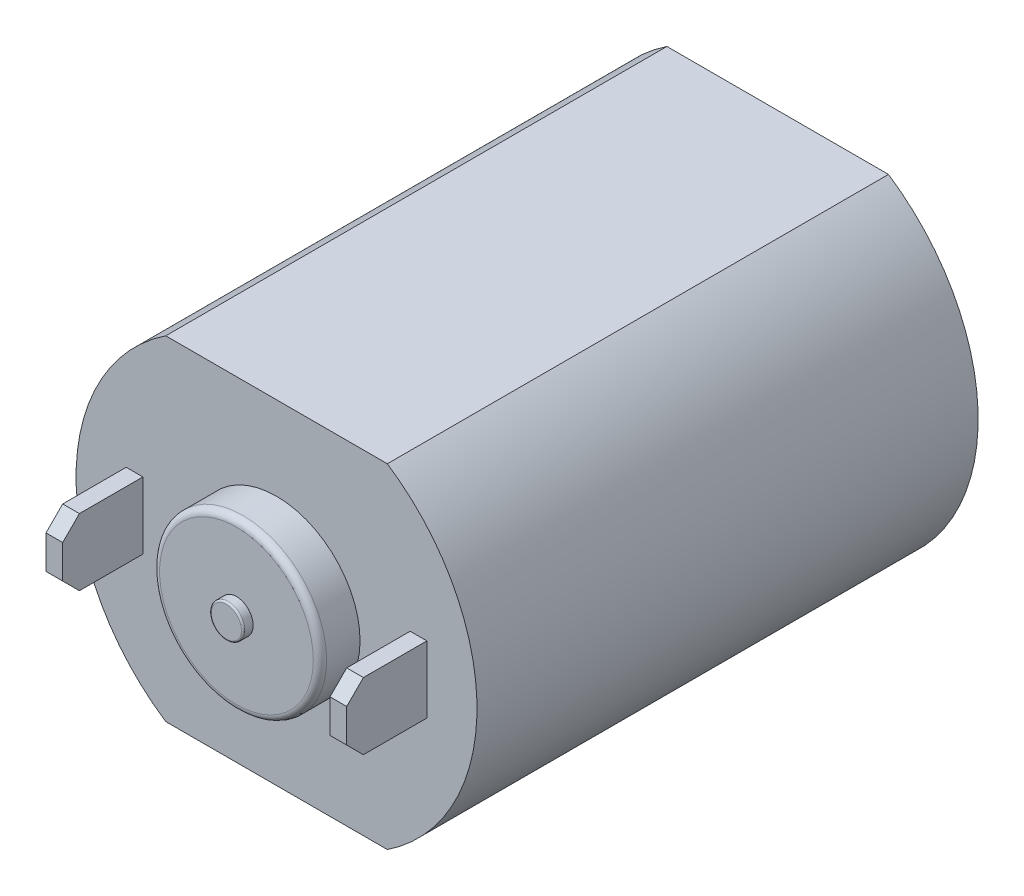
SolidWorks part; units mm, degrees
ref_plane "前视基准面" through (0, 0, 0) normal (0, 0, 1) x (1, 0, 0)
ref_plane "上视基准面" through (0, 0, 0) normal (0, 1, 0) x (1, 0, 0)
ref_plane "右视基准面" through (0, 0, 0) normal (1, 0, 0) x (0, 0, -1)
sketch "草图1" plane through (0, 0, 0) normal (0, 0, 1) x (1, 0, 0)
  circle A0 centre (0, 0) radius 6
extrude "凸台-拉伸1" add sketch "草图1" along normal blind 15 contours A0
sketch "草图6" plane through (0, 0, 0) normal (0, 0, -1) x (-1, 0, 0)
  line L0 (-5.8948, 0) -> (4.7099, 0) construction
  line L1 (-3.3166, 5) -> (3.3166, 5)
  line L2 (-3.3166, -5) -> (3.3166, -5)
  circle A0 centre (0, 0) radius 6 construction
  arc A1 (-3.3166, 5) -> (3.3166, 5) centre (0, 0) cw
  arc A2 (-3.3166, -5) -> (3.3166, -5) centre (0, 0) ccw
extrude "切除-拉伸1" cut sketch "草图6" against normal blind 15
sketch "草图7" plane through (0, 0, 15) normal (0, 0, 1) x (1, 0, 0)
  circle A0 centre (0, 0) radius 2.5
extrude "凸台-拉伸2" add sketch "草图7" along normal blind 1.2
fillet "圆角1" radius 0.2 1 edges at (2.5, 0, 16.2)
sketch "草图8" plane through (0, 0, 16.2) normal (0, 0, 1) x (1, 0, 0)
  circle A0 centre (0, 0) radius 0.5
extrude "凸台-拉伸3" add sketch "草图8" along normal blind 0.3
fillet "圆角2" radius 0.05 1 edges at (0.5, 0, 16.5)
sketch "草图9" plane through (0, 0, 15) normal (0, 0, 1) x (1, 0, 0)
  line L0 (0, 0) -> (0, 4.6934) construction
  line L1 (4, 0) -> (4, 1)
  line L2 (4, 1) -> (4.5, 1)
  line L3 (4.5, 1) -> (4.5, -1)
  line L4 (4.5, -1) -> (4, -1)
  line L5 (4, -1) -> (4, 0)
  line L6 (-4, -1) -> (-4, 0)
  line L7 (-4.5, -1) -> (-4, -1)
  line L8 (-4.5, 1) -> (-4.5, -1)
  line L9 (-4, 1) -> (-4.5, 1)
  line L10 (-4, 0) -> (-4, 1)
  dimension "D1" = 0.5
  dimension "D2" = 1
  dimension "D3" = 1
extrude "凸台-拉伸4" add sketch "草图9" along normal blind 2.4
chamfer "倒角1" distance 0.5 1 edges at (-4.25, 1, 17.4)
chamfer "倒角2" distance 0.5 1 edges at (-4.25, -1, 17.4)
chamfer "倒角3" distance 0.5 2 edges at (4.25, -1, 17.4) (4.25, 1, 17.4)
sketch "草图10" plane through (0, 0, 0) normal (0, 0, -1) x (-1, 0, 0)
  circle A0 centre (0, 0) radius 2
extrude "凸台-拉伸5" add sketch "草图10" along normal blind 0.1
